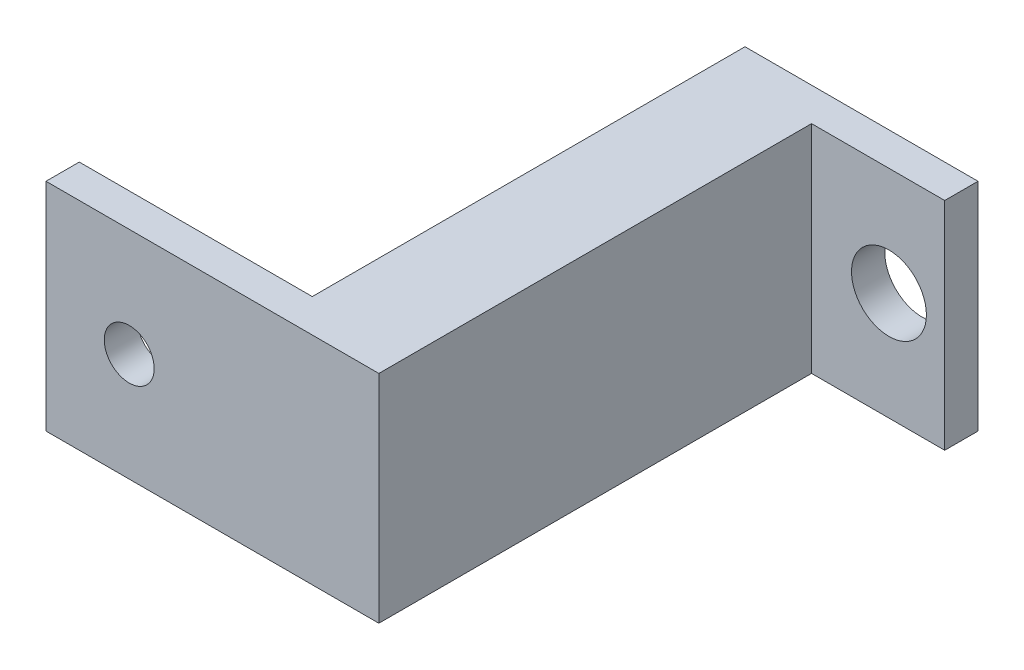
SolidWorks part; units mm, degrees
ref_plane "Płaszczyzna przednia" through (0, 0, 0) normal (0, 0, 1) x (1, 0, 0)
ref_plane "Płaszczyzna górna" through (0, 0, 0) normal (0, 1, 0) x (1, 0, 0)
ref_plane "Płaszczyzna prawa" through (0, 0, 0) normal (1, 0, 0) x (0, 0, -1)
sketch "Szkic1" plane through (0, 0, 0) normal (0, 0, 1) x (1, 0, 0)
  line L1 (-7, -6.5) -> (7, -6.5)
  line L2 (-7, -6.5) -> (-7, 6.5)
  line L3 (-7, 6.5) -> (7, 6.5)
  line L4 (7, -6.5) -> (7, 6.5)
  line L5 (-7, -6.5) -> (7, 6.5) construction
  line L6 (-7, 6.5) -> (7, -6.5) construction
  circle A0 centre (3.65, 0) radius 2.25
  point P0 (0, 0)
  dimension "D3" = 4.5
  dimension "D4" = 3.35
  dimension "D5" = 6.5
  dimension "D1" = 13
  dimension "D2" = 14
extrude "Dodanie-wyciągnięcie1" add sketch "Szkic1" along normal blind 2
sketch "Szkic2" plane through (0, 0, 2) normal (0, 0, 1) x (1, 0, 0)
  line L0 (-7, -6.5) -> (7, -6.5) construction
  line L1 (-7, 6.5) -> (-1, 6.5)
  line L2 (-7, 6.5) -> (-7, -6.5)
  line L3 (-7, -6.5) -> (-1, -6.5)
  line L4 (-1, 6.5) -> (-1, -6.5)
  dimension "D1" = 6
extrude "Dodanie-wyciągnięcie2" add sketch "Szkic2" along normal blind 24
sketch "Szkic3" plane through (0, 0, 26) normal (0, 0, 1) x (1, 0, 0)
  line L1 (-1, 6.5) -> (-21, 6.5)
  line L2 (-1, 6.5) -> (-1, -6.5)
  line L3 (-1, -6.5) -> (-21, -6.5)
  line L4 (-21, 6.5) -> (-21, -6.5)
  circle A0 centre (-16, 0) radius 1.5
  dimension "D2" = 3
  dimension "D3" = 5
  dimension "D4" = 6.5
  dimension "D1" = 20
extrude "Dodanie-wyciągnięcie3" add sketch "Szkic3" along normal blind 2
